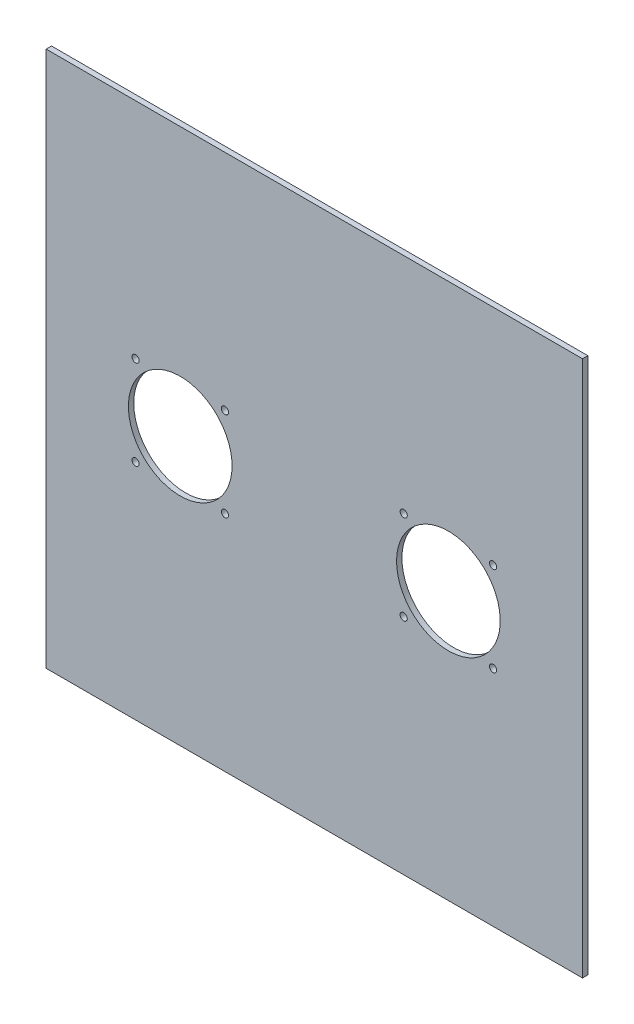
SolidWorks part; units mm, degrees
ref_plane "Alzado" through (0, 0, 0) normal (0, 0, 1) x (1, 0, 0)
ref_plane "Planta" through (0, 0, 0) normal (0, 1, 0) x (1, 0, 0)
ref_plane "Vista lateral" through (0, 0, 0) normal (1, 0, 0) x (0, 0, -1)
sketch "Croquis1" plane through (0, 0, 0) normal (0, 0, 1) x (1, 0, 0)
  line L6 (0, 0) -> (300, 0)
  line L7 (0, 0) -> (0, 300)
  line L8 (0, 300) -> (300, 300)
  line L9 (300, 0) -> (300, 300)
  dimension "D1" = 300
  dimension "D2" = 300
extrude "Saliente-Extruir1" add sketch "Croquis1" along normal blind 3
sketch "Croquis2" plane through (0, 0, 3) normal (0, 0, 1) x (1, 0, 0)
  line L36 (150, 300) -> (150, 0) construction
  line L70 (300, 300) -> (0, 300) construction
  line L71 (0, 0) -> (300, 0) construction
  line L72 (150, 150) -> (0, 150) construction
  line L74 (0, 300) -> (0, 0) construction
  line L76 (75, 285.2994) -> (75, 0) construction
  circle A0 centre (50, 175) radius 2
  circle A1 centre (100, 175) radius 2
  circle A2 centre (100, 125) radius 2
  circle A3 centre (50, 125) radius 2
  circle A4 centre (75, 150) radius 29
  circle A5 centre (200, 125) radius 2
  circle A6 centre (250, 125) radius 2
  circle A7 centre (200, 175) radius 2
  circle A8 centre (225, 150) radius 29
  circle A9 centre (250, 175) radius 2
  dimension "D1" = 4
  dimension "D4" = 58
  dimension "D2" = 25
  dimension "D3" = 25
extrude "Cortar-Extruir1" cut sketch "Croquis2" against normal blind 10
